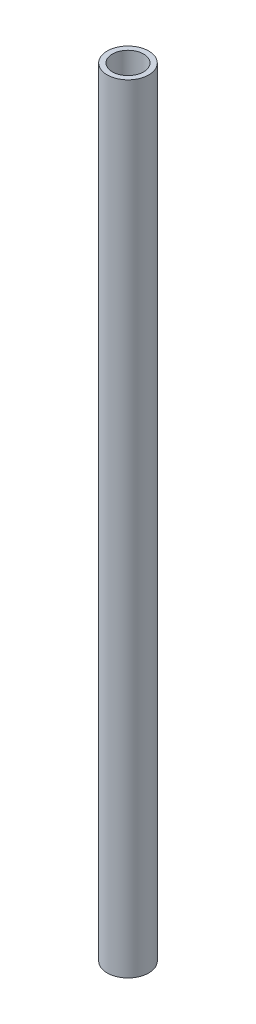
SolidWorks part; units mm, degrees
ref_plane "Front Plane" through (0, 0, 0) normal (0, 0, 1) x (1, 0, 0)
ref_plane "Top Plane" through (0, 0, 0) normal (0, 1, 0) x (1, 0, 0)
ref_plane "Right Plane" through (0, 0, 0) normal (1, 0, 0) x (0, 0, -1)
sketch "Sketch1" plane through (0, 0, 0) normal (0, 1, 0) x (1, 0, 0)
  circle A0 centre (0, 0) radius 8
  circle A1 centre (0, 0) radius 6
extrude "Boss-Extrude1" add sketch "Sketch1" along normal blind 300
